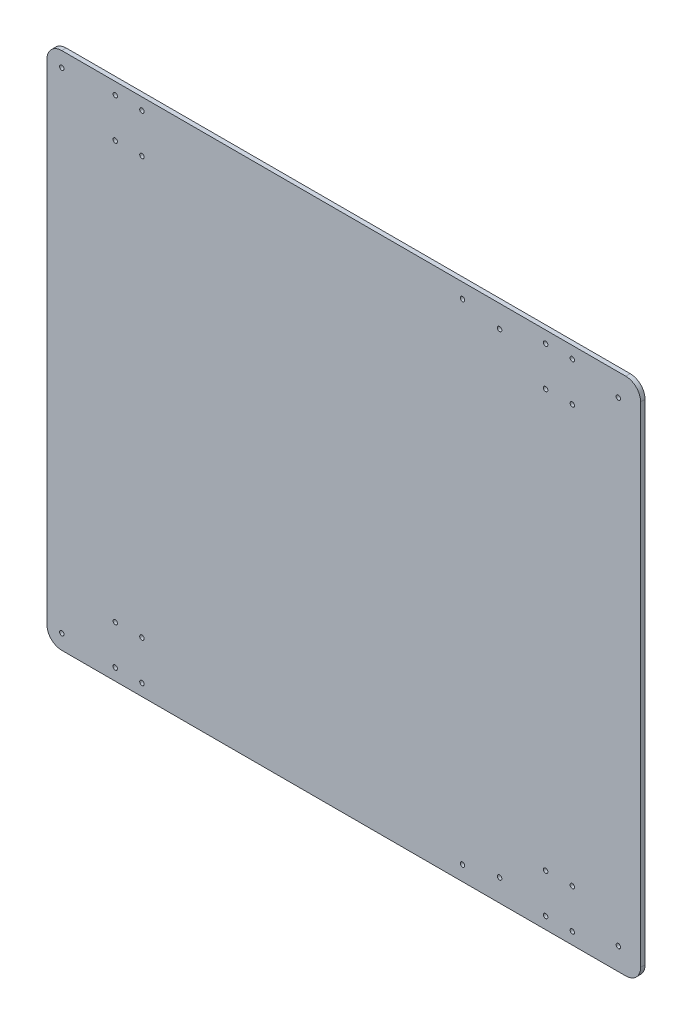
SolidWorks part; units mm, degrees
ref_plane "Plan de face" through (0, 0, 0) normal (0, 0, 1) x (1, 0, 0)
ref_plane "Plan de dessus" through (0, 0, 0) normal (0, 1, 0) x (1, 0, 0)
ref_plane "Plan de droite" through (0, 0, 0) normal (1, 0, 0) x (0, 0, -1)
sketch "Esquisse1" plane through (0, 0, 0) normal (0, 0, 1) x (1, 0, 0)
  line L1 (10, 0) -> (390, 0)
  line L2 (0, 10) -> (0, 340)
  line L3 (10, 350) -> (390, 350)
  line L4 (400, 10) -> (400, 340)
  line L8 (23, 327) -> (302, 327) construction
  line L9 (302, 327) -> (302, 23) construction
  line L10 (302, 23) -> (23, 23) construction
  line L11 (23, 23) -> (23, 327) construction
  line L12 (400, 175) -> (302, 175) construction
  line L13 (385, 15) -> (305, 15) construction
  line L14 (345, 15) -> (345, 0) construction
  line L15 (354, 15) -> (354, 0) construction
  line L16 (336, 15) -> (336, 0) construction
  line L17 (354, 15) -> (354, 41.7849) construction
  line L18 (336, 15) -> (336, 41.7849) construction
  line L19 (200, 350) -> (200, 0) construction
  line L20 (0, 175) -> (200, 175) construction
  arc A0 (390, 0) -> (400, 10) centre (390, 10) ccw
  arc A1 (10, 0) -> (0, 10) centre (10, 10) cw
  arc A2 (0, 340) -> (10, 350) centre (10, 340) cw
  arc A3 (390, 350) -> (400, 340) centre (390, 340) cw
  circle A4 centre (385, 15) radius 1.5
  circle A5 centre (305, 15) radius 1.5
  circle A6 centre (305, 335) radius 1.5
  circle A7 centre (385, 335) radius 1.5
  circle A12 centre (354, 8) radius 1.5
  circle A13 centre (336, 8) radius 1.5
  circle A14 centre (336, 34.48) radius 1.5
  circle A15 centre (354, 34.48) radius 1.5
  circle A16 centre (336, 342) radius 1.5
  circle A17 centre (336, 315.52) radius 1.5
  circle A18 centre (354, 315.52) radius 1.5
  circle A19 centre (354, 342) radius 1.5
  circle A20 centre (64, 34.48) radius 1.5
  circle A21 centre (46, 34.48) radius 1.5
  circle A22 centre (46, 8) radius 1.5
  circle A23 centre (64, 8) radius 1.5
  circle A24 centre (46, 315.52) radius 1.5
  circle A25 centre (46, 342) radius 1.5
  circle A26 centre (64, 342) radius 1.5
  circle A27 centre (64, 315.52) radius 1.5
  point P7 (400, 0)
  point P10 (0, 0)
  point P13 (0, 350)
  dimension "D3" = 10
  dimension "D8" = 3
  dimension "D9" = 3
  dimension "D10" = 3
  dimension "D11" = 3
  dimension "D17" = 15
  dimension "D18" = 15
  dimension "D19" = 95
  dimension "D20" = 95
  dimension "D25" = 3
  dimension "D26" = 3
  dimension "D27" = 3
  dimension "D28" = 3
  dimension "D1" = 350
  dimension "D2" = 400
  dimension "D13" = 15
  dimension "D14" = 15
  dimension "D15" = 15
  dimension "D16" = 15
  dimension "D21" = 9
  dimension "D22" = 9
  dimension "D23" = 8
  dimension "D24" = 8
  dimension "D29" = 26.48
  dimension "D30" = 26.48
  dimension "D31" = 18
extrude "Boss.-Extru.2" add sketch "Esquisse1" along normal blind 3
sketch "Esquisse2" plane through (0, 0, 0) normal (0, 0, -1) x (-1, 0, 0)
  line L0 (-10, 350) -> (-390, 350) construction
  line L1 (-10, 0) -> (-390, 0) construction
  line L2 (-295, 350) -> (-295, 0) construction
  line L3 (-10, 350) -> (-390, 350) construction
  line L4 (-10, 0) -> (-390, 0) construction
  line L5 (0, 10) -> (0, 340) construction
  circle A0 centre (-10, 10) radius 1.5
  circle A1 centre (-10, 340) radius 1.5
  circle A2 centre (-280, 340) radius 1.5
  circle A3 centre (-280, 10) radius 1.5
  point P22 (0, 175)
  dimension "D1" = 3
  dimension "D2" = 3
  dimension "D3" = 3
  dimension "D4" = 3
  dimension "D5" = 270
  dimension "D6" = 270
  dimension "D7" = 10
  dimension "D8" = 10
  dimension "D9" = 10
  dimension "D10" = 295
  dimension "D11" = 15
  dimension "D12" = 10
extrude "Enlèv. mat.-Extru.1" cut sketch "Esquisse2" against normal blind 10
